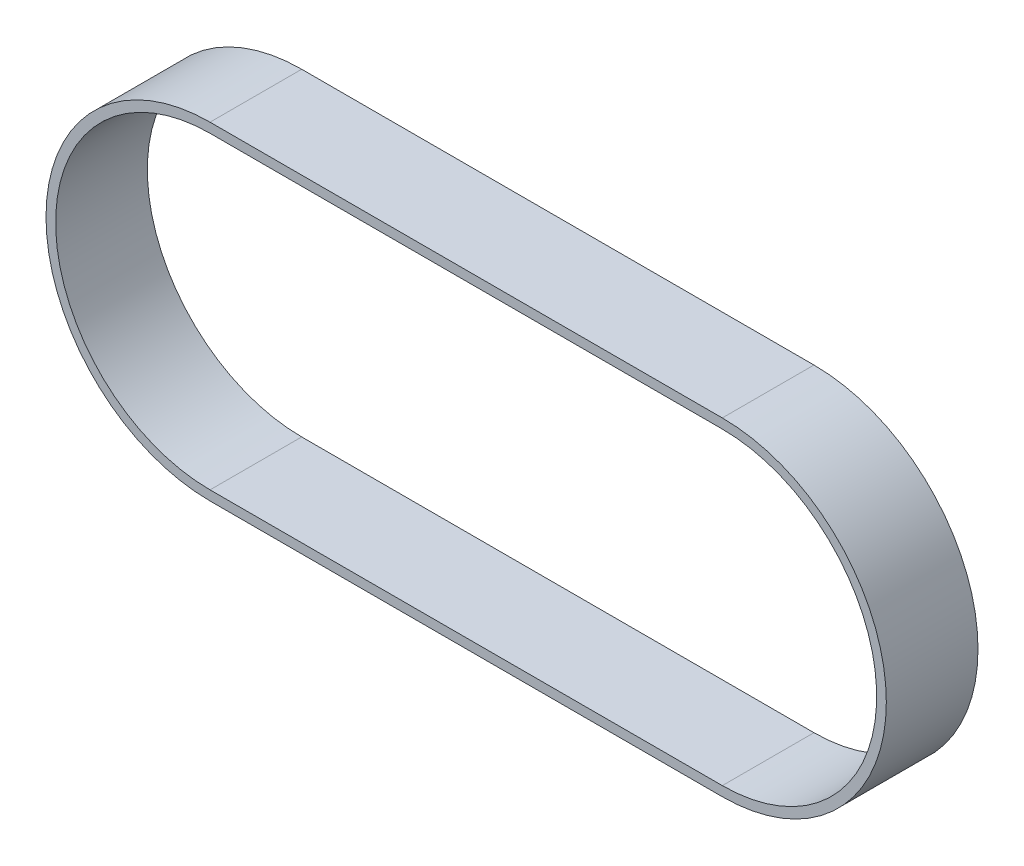
SolidWorks part; units mm, degrees
ref_plane "Front Plane" through (0, 0, 0) normal (0, 0, 1) x (1, 0, 0)
ref_plane "Top Plane" through (0, 0, 0) normal (0, 1, 0) x (1, 0, 0)
ref_plane "Right Plane" through (0, 0, 0) normal (1, 0, 0) x (0, 0, -1)
sketch "Sketch2" plane through (0, 0, 0) normal (0, 0, 1) x (1, 0, 0)
  line L0 (0, 0) -> (1, 0) construction
  line L1 (0, 0) -> (0, 1) construction
  line L2 (0, -32) -> (-106.18, -32)
  line L3 (-106.18, 32) -> (0, 32)
  arc A0 (0, 32) -> (0, -32) centre (0, 0) cw
  arc A1 (-106.18, -32) -> (-106.18, 32) centre (-106.18, 0) cw
extrude "Extrude-Thin1" add sketch "Sketch2" along normal blind 9.5 and the other way blind 9.5 thin thin type one direction wall 2
